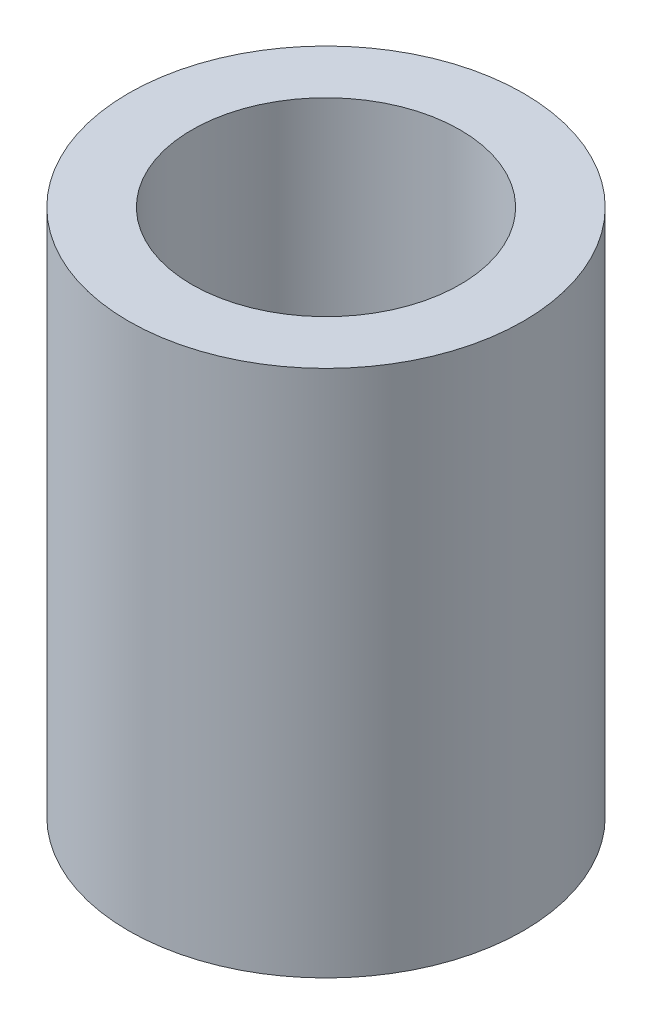
SolidWorks part; units mm, degrees
ref_plane "Front Plane" through (0, 0, 0) normal (0, 0, 1) x (1, 0, 0)
ref_plane "Top Plane" through (0, 0, 0) normal (0, 1, 0) x (1, 0, 0)
ref_plane "Right Plane" through (0, 0, 0) normal (1, 0, 0) x (0, 0, -1)
sketch "Sketch1" plane through (0, 0, 0) normal (0, 0, 1) x (1, 0, 0)
  line L1 (-2.4, 5) -> (-2.4, 0)
  line L2 (-2.4, 0) -> (-9.35, 0)
  line L3 (-9.35, 0) -> (-9.35, 25)
  line L4 (-9.35, 25) -> (-6.35, 25)
  line L5 (-6.35, 25) -> (-6.35, 5)
  line L6 (-6.35, 5) -> (-2.4, 5)
  line L8 (0, 0) -> (0, -27.8391) construction
  point P8 (-2.4, 2.2407)
  point P9 (0, 0)
  point P11 (0, 0)
  dimension "D1" = 12.7
  dimension "D2" = 4.8
  dimension "D3" = 5
  dimension "D4" = 20
  dimension "D5" = 3
revolve "Revolve1" add sketch "Sketch1" angle 360 about L8
equation "\"m3 hole\"= 3.2"
equation "\"m4 hole\"= 4.2"
equation "\"m5 hole\"= 5.2"
equation "\"m6 hole\"= 6.2"
equation "\"m8 hole\"= 8.2"
equation "\"m3 tapped\"= 2.5"
equation "\"m4 tapped\"= 3.3"
equation "\"m5 tapped\"= 4.2"
equation "\"m6 tapped\"= 5"
equation "\"m8 tapped\"= 6.8"
